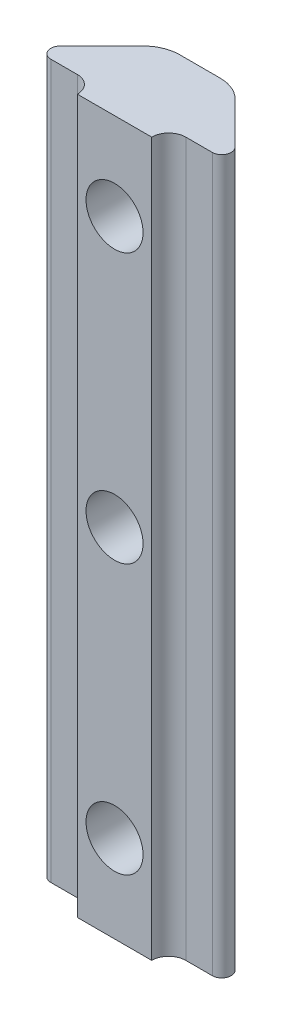
SolidWorks part; units mm, degrees
ref_plane "Front Plane" through (0, 0, 0) normal (0, 0, 1) x (1, 0, 0)
ref_plane "Top Plane" through (0, 0, 0) normal (0, 1, 0) x (1, 0, 0)
ref_plane "Right Plane" through (0, 0, 0) normal (1, 0, 0) x (0, 0, -1)
sketch "Sketch1" plane through (0, 0, 0) normal (0, 1, 0) x (1, 0, 0)
  line L10 (-2.9785, -6.8393) -> (2.9785, -6.8393)
  line L14 (6.4748, -5.4744) -> (4.3434, -5.4744)
  line L15 (3.6793, -0.8538) -> (7.0094, -4.1838)
  line L16 (-1.6181, 0) -> (1.6181, 0)
  line L17 (-7.0094, -4.1838) -> (-3.6793, -0.8538)
  line L18 (-4.3434, -5.4744) -> (-6.4748, -5.4744)
  arc A6 (4.3434, -5.4744) -> (2.9785, -6.8393) centre (4.3434, -6.8393) ccw
  arc A7 (6.4748, -5.4744) -> (7.0094, -4.1838) centre (6.4748, -4.7184) ccw
  arc A8 (3.6793, -0.8538) -> (1.6181, 0) centre (1.6181, -2.915) ccw
  arc A9 (-1.6181, 0) -> (-3.6793, -0.8538) centre (-1.6181, -2.915) ccw
  arc A10 (-7.0094, -4.1838) -> (-6.4748, -5.4744) centre (-6.4748, -4.7184) ccw
  arc A11 (-2.9785, -6.8393) -> (-4.3434, -5.4744) centre (-4.3434, -6.8393) ccw
  point P0 (0, 0)
extrude "Boss-Extrude1" add sketch "Sketch1" along normal blind 57.15
sketch "Sketch2" plane through (0, 0, 6.8393) normal (0, 0, 1) x (1, 0, 0)
  line L0 (0, 57.15) -> (0, 0) construction
  line L1 (-2.9785, 57.15) -> (2.9785, 57.15) construction
  circle A0 centre (0, 50.165) radius 2.286
  circle A1 centre (0, 28.575) radius 2.286
  circle A2 centre (0, 6.985) radius 2.286
  dimension "D3" = 4.572
  dimension "D4" = 4.572
  dimension "D5" = 4.572
  dimension "D1" = 21.59
  dimension "D2" = 21.59
extrude "Cut-Extrude1" cut sketch "Sketch2" against normal through all
sketch "Sketch3" plane through (0, 0, 6.8393) normal (0, 0, 1) x (1, 0, 0)
  circle A0 centre (0, 28.575) radius 5.3514
extrude "Cut-Extrude2" [suppressed] cut sketch "Sketch3" against normal blind 2.54
